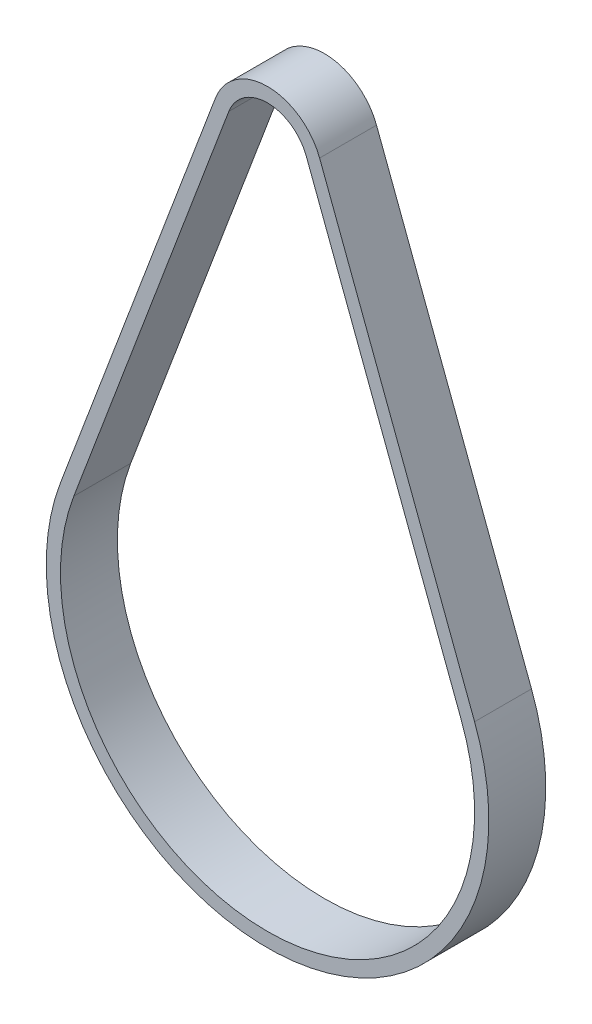
SolidWorks part; units mm, degrees
material "Caucho de silicio"
ref_plane "Alzado" through (0, 0, 0) normal (0, 0, 1) x (1, 0, 0)
ref_plane "Planta" through (0, 0, 0) normal (0, 1, 0) x (1, 0, 0)
ref_plane "Vista lateral" through (0, 0, 0) normal (1, 0, 0) x (0, 0, -1)
sketch "Croquis1" plane through (0, 0, 0) normal (0, 0, 1) x (1, 0, 0)
  line L0 (-5.4451, 28.8614) -> (-27.2302, -28.8614)
  line L1 (0, -55.4784) -> (0, 55.4784) construction
  line L2 (5.4451, 28.8614) -> (27.2302, -28.8614)
  line L3 (32.0155, 0) -> (-32.0155, 0) construction
  line L4 (-7.3163, 29.5676) -> (-29.1014, -28.1552)
  line L5 (7.3163, 29.5676) -> (29.1014, -28.1552)
  arc A0 (5.4451, 28.8614) -> (-5.4451, 28.8614) centre (0, 26.8064) ccw
  arc A1 (-27.2302, -28.8614) -> (27.2302, -28.8614) centre (0, -39.1384) ccw
  arc A2 (-29.1014, -28.1552) -> (29.1014, -28.1552) centre (0, -39.1384) ccw
  arc A3 (7.3163, 29.5676) -> (-7.3163, 29.5676) centre (0, 26.8064) ccw
  point P1 (-16.3377, 0)
  dimension "D1" = 58.21
  dimension "D2" = 11.64
  dimension "D3" = 61.697
  dimension "D4" = 2
extrude "Saliente-Extruir1" add sketch "Croquis1" along normal blind 8
